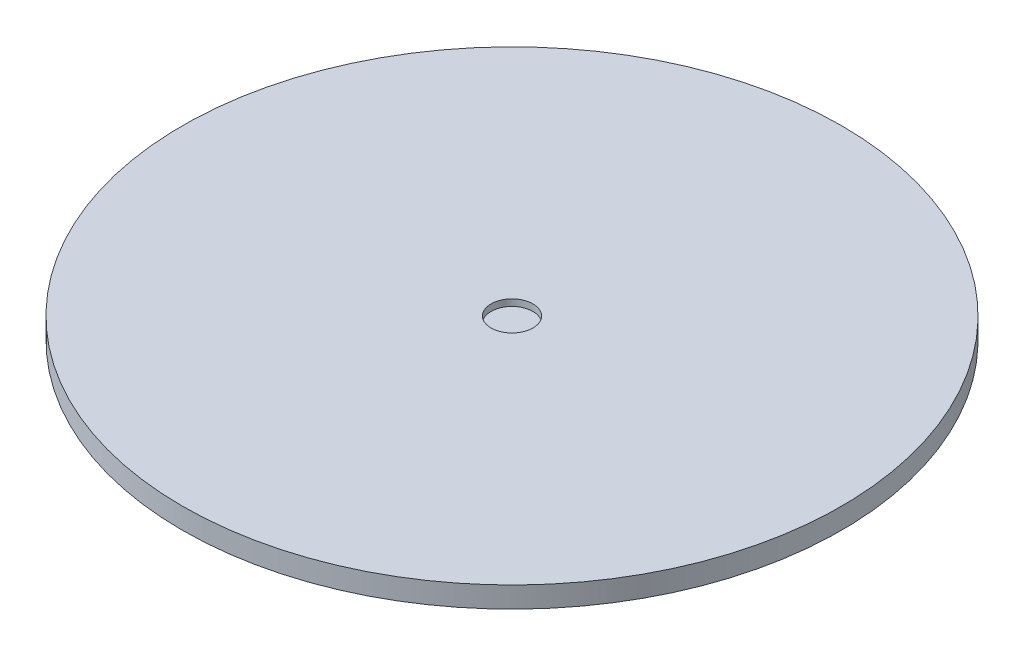
SolidWorks part; units mm, degrees
material "Acrylic (Medium-high impact)"
ref_plane "Front Plane" through (0, 0, 0) normal (0, 0, 1) x (1, 0, 0)
ref_plane "Top Plane" through (0, 0, 0) normal (0, 1, 0) x (1, 0, 0)
ref_plane "Right Plane" through (0, 0, 0) normal (1, 0, 0) x (0, 0, -1)
sketch "Sketch1" plane through (0, 0, 0) normal (0, 1, 0) x (1, 0, 0)
  circle A0 centre (0, 0) radius 100
  dimension "D1" = 200
extrude "Boss-Extrude1" add sketch "Sketch1" along normal blind 6.35
sketch "Sketch3" plane through (0, 6.35, 0) normal (0, 1, 0) x (1, 0, 0)
  circle A0 centre (0, 0) radius 6.35
  dimension "D1" = 12.7
extrude "Cut-Extrude1" cut sketch "Sketch3" against normal blind 2
